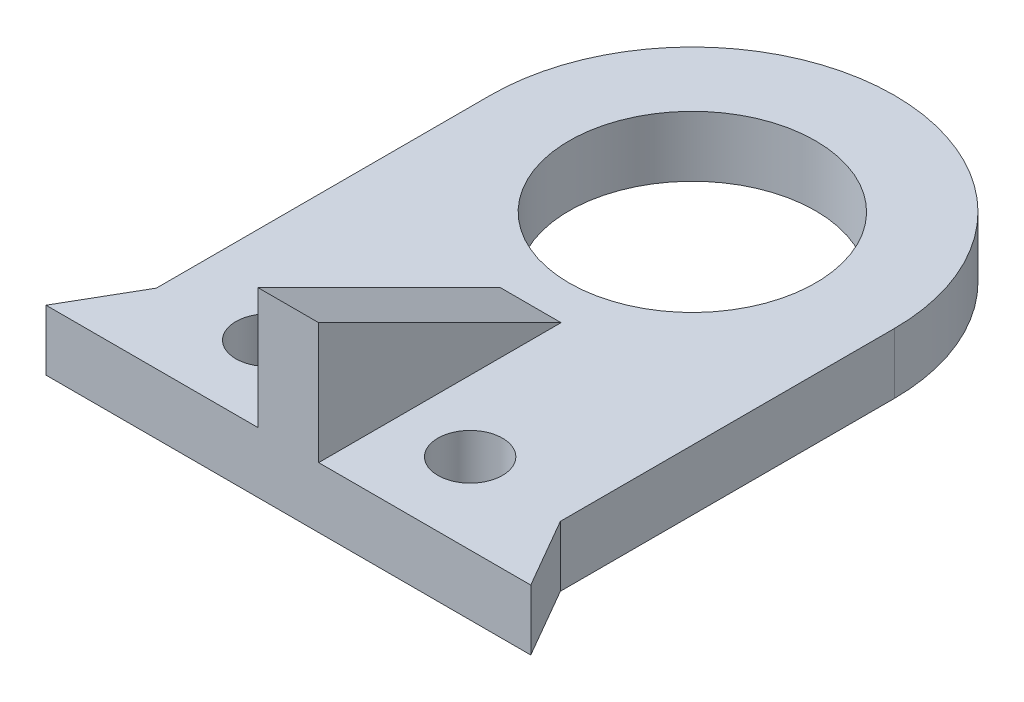
SolidWorks part; units mm, degrees
ref_plane "Front Plane" through (0, 0, 0) normal (0, 0, 1) x (1, 0, 0)
ref_plane "Top Plane" through (0, 0, 0) normal (0, 1, 0) x (1, 0, 0)
ref_plane "Right Plane" through (0, 0, 0) normal (1, 0, 0) x (0, 0, -1)
sketch "Sketch1" plane through (0, 0, 0) normal (0, 1, 0) x (1, 0, 0)
  line L1 (-10, -10) -> (10, -10)
  line L2 (-10, -10) -> (-10, 10)
  line L4 (10, -10) -> (10, 10)
  line L5 (-10, -10) -> (10, 10) construction
  line L6 (-10, 10) -> (10, -10) construction
  arc A0 (10, 10) -> (-10, 10) centre (0, 10) ccw
  circle A1 centre (0, 10) radius 6.1
  point P0 (0, 0)
  dimension "D3" = 12.2
  dimension "D1" = 20
  dimension "D2" = 20
extrude "Boss-Extrude1" add sketch "Sketch1" along normal blind 3
sketch "Sketch2" plane through (0, 3, 0) normal (0, 1, 0) x (1, 0, 0)
  line L0 (-10, 10) -> (-10, -10) construction
  line L1 (10, -10) -> (10, 10) construction
  line L2 (-10, -10) -> (10, -10) construction
  circle A0 centre (-5, -6) radius 1.6
  circle A1 centre (5, -6) radius 1.6
  dimension "D1" = 3.2
  dimension "D2" = 3.2
  dimension "D3" = 5
  dimension "D4" = 5
  dimension "D5" = 4
  dimension "D6" = 4
extrude "Cut-Extrude1" cut sketch "Sketch2" against normal through all
sketch "Sketch4" plane through (0, 0, 0) normal (1, 0, 0) x (0, 0, -1)
  line L0 (-10, 3) -> (-10, 9)
  line L1 (-10, 9) -> (2, 3)
  line L2 (-10, 3) -> (10, 3) construction
  line L3 (-10, 3) -> (2, 3)
  dimension "D1" = 6
  dimension "D2" = 12
extrude "Boss-Extrude2" add sketch "Sketch4" along normal mid plane 3
sketch "Sketch5" plane through (0, 0, 0) normal (0, 1, 0) x (1, 0, 0)
  line L0 (-10, -10) -> (-12, -10)
  line L1 (-12, -10) -> (-10, -6.5359)
  line L2 (-10, 10) -> (-10, -10) construction
  line L3 (-10, -6.5359) -> (-10, -10)
  line L4 (0, 0) -> (0, -5.3772) construction
  line L5 (10, -10) -> (12, -10)
  line L6 (12, -10) -> (10, -6.5359)
  line L7 (10, -6.5359) -> (10, -10)
  dimension "D1" = 2
  dimension "D2" = 60
extrude "Boss-Extrude3" add sketch "Sketch5" along normal blind 3
